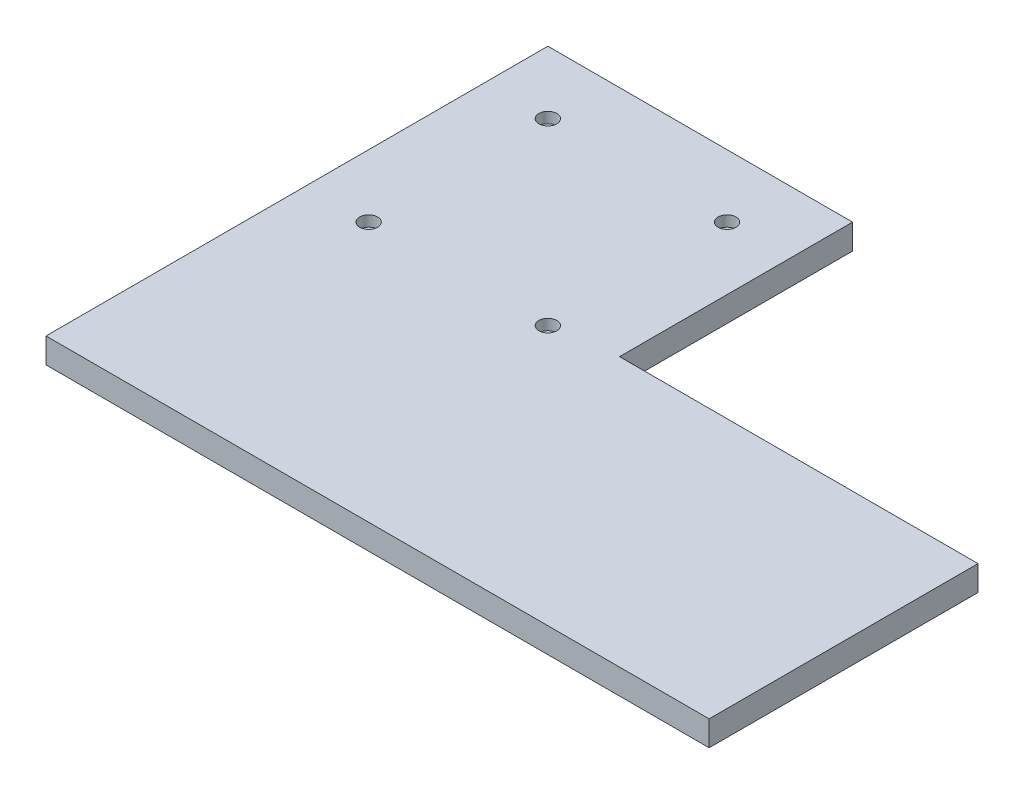
SolidWorks part; units mm, degrees
ref_plane "Front Plane" through (0, 0, 0) normal (0, 0, 1) x (1, 0, 0)
ref_plane "Top Plane" through (0, 0, 0) normal (0, 1, 0) x (1, 0, 0)
ref_plane "Right Plane" through (0, 0, 0) normal (1, 0, 0) x (0, 0, -1)
sketch "Sketch1" plane through (0, 0, 0) normal (0, 1, 0) x (1, 0, 0)
  line L0 (14.3183, 31.8949) -> (-70.6817, 31.8949)
  line L1 (-70.6817, 31.8949) -> (-70.6817, -108.1051)
  line L2 (-70.6817, -108.1051) -> (114.3183, -108.1051)
  line L3 (114.3183, -108.1051) -> (114.3183, -33.1051)
  line L4 (114.3183, -33.1051) -> (14.3183, -33.1051)
  line L5 (14.3183, -33.1051) -> (14.3183, 31.8949)
  dimension "D1" = 65
  dimension "D2" = 85
  dimension "D3" = 140
  dimension "D4" = 185
extrude "Boss-Extrude1" add sketch "Sketch1" along normal blind 7 contours L5 L0 L1 L2 L3 L4
ref_plane "Plane1" through (0, 7, 0) normal (0, 1, 0) x (1, 0, 0)
sketch "Sketch2" plane through (0, 7, 0) normal (0, 1, 0) x (1, 0, 0)
  line L0 (14.3183, 31.8949) -> (-70.6817, 31.8949) construction
  line L1 (-58.1817, 19.3949) -> (1.8183, 19.3949)
  line L2 (-58.1817, 19.3949) -> (-58.1817, -40.6051)
  line L3 (-58.1817, -40.6051) -> (1.8183, -40.6051)
  line L4 (1.8183, 19.3949) -> (1.8183, -40.6051)
  line L5 (-70.6817, 31.8949) -> (-70.6817, -108.1051) construction
  line L6 (-53.1817, 19.3949) -> (-53.1817, -40.6051) construction
  line L7 (-58.1817, 14.3949) -> (1.8183, 14.3949) construction
  line L8 (-58.1817, -10.6051) -> (1.8183, -10.6051) construction
  circle A0 centre (-53.1817, 14.3949) radius 2.5
  circle A1 centre (-3.1817, 14.3949) radius 2.5
  circle A2 centre (-3.1817, -35.6051) radius 2.5
  circle A3 centre (-53.1817, -35.6051) radius 2.5
  dimension "D7" = 2
  dimension "D1" = 60
  dimension "D2" = 60
  dimension "D3" = 12.5
  dimension "D4" = 12.5
  dimension "D5" = 5
  dimension "D6" = 5
extrude "Cut-Extrude2" cut sketch "Sketch2" against normal blind 3 contours A0 | A2 | A3 | A1
